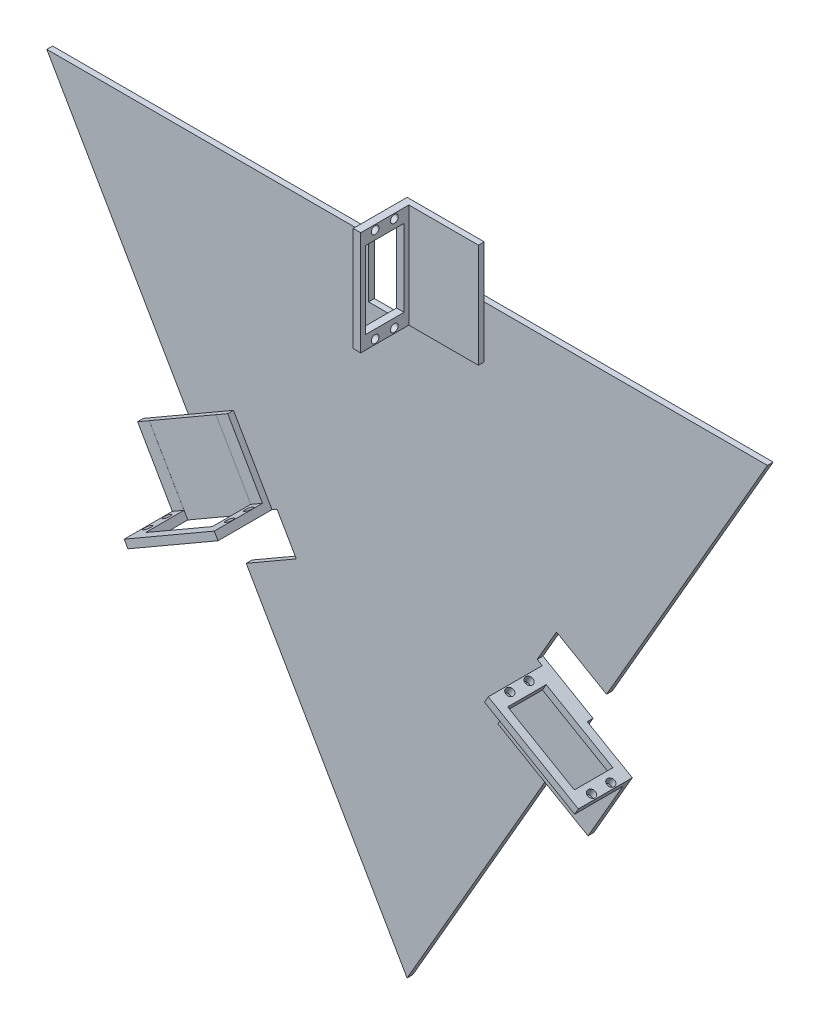
SolidWorks part; units mm, degrees
ref_plane "Front Plane" through (0, 0, 0) normal (0, 0, 1) x (1, 0, 0)
ref_plane "Top Plane" through (0, 0, 0) normal (0, 1, 0) x (1, 0, 0)
ref_plane "Right Plane" through (0, 0, 0) normal (1, 0, 0) x (0, 0, -1)
sketch "Sketch2" plane through (0, 0, 0) normal (0, 0, 1) x (1, 0, 0)
  line L0 (0, 161.9468) -> (0, -161.9468) construction
  line L1 (-187, 161.9468) -> (187, 161.9468)
  line L2 (187, 161.9468) -> (0, -161.9468)
  line L3 (-187, 161.9468) -> (0, -161.9468)
  point P4 (0, 0)
  point P8 (0, 161.9468)
  dimension "D1" = 374
  dimension "D2" = 374
  dimension "D3" = 374
extrude "Boss-Extrude1" add sketch "Sketch2" along normal blind 3
sketch "Sketch4" plane through (0, 0, 3) normal (0, 0, 1) x (1, 0, 0)
  line L0 (0, 0) -> (-187, 161.9468) construction
  line L2 (0, 0) -> (0, -161.9468) construction
  line L3 (187, 161.9468) -> (0, -161.9468) construction
  line L4 (116.8827, -13.5) -> (96.8827, -48.141)
  line L6 (70.1173, 13.5) -> (116.8827, -13.5)
  line L7 (70.1173, 13.5) -> (50.1173, -21.141)
  line L8 (73.5, -34.641) -> (28.9418, -111.818) construction
  line L9 (50.1173, -21.141) -> (96.8827, -48.141)
  line L10 (0, 0) -> (187, 161.9468) construction
  line L11 (0, -161.9468) -> (-187, 161.9468) construction
  line L12 (-116.8827, -13.5) -> (-136.8827, 21.141)
  line L13 (-70.1173, 13.5) -> (-116.8827, -13.5)
  line L14 (-70.1173, 13.5) -> (-90.1173, 48.141)
  line L15 (-90.1173, 48.141) -> (-136.8827, 21.141)
  line L20 (-187, 161.9468) -> (187, 161.9468) construction
  line L21 (40, 134.9468) -> (0, 134.9468)
  line L22 (40, 188.9468) -> (40, 134.9468)
  line L23 (40, 188.9468) -> (0, 188.9468)
  line L24 (0, 188.9468) -> (0, 134.9468)
  point P13 (-93.5, 0)
  point P16 (93.5, 0)
  point P18 (93.5, 0)
  point P25 (-93.5, 0)
  point P29 (0, 161.9468)
  point P30 (0, 161.9468)
  dimension "D1" = 40
  dimension "D2" = 54
  dimension "D3" = 54
  dimension "D4" = 40
  dimension "D5" = 54
  dimension "D6" = 40
extrude "Boss-Extrude2" add sketch "Sketch4" along normal blind 3
sketch "Sketch11" plane through (0, 0, 6) normal (0, 0, 1) x (1, 0, 0)
  line L0 (93.5, 0) -> (73.5, -34.641) construction
  line L1 (116.8827, -13.5) -> (70.1173, 13.5) construction
  line L2 (116.8827, -13.5) -> (114.9327, -16.8775)
  line L3 (96.8827, -48.141) -> (116.8827, -13.5) construction
  line L4 (114.9327, -16.8775) -> (68.1673, 10.1225)
  line L5 (70.1173, 13.5) -> (50.1173, -21.141) construction
  line L6 (68.1673, 10.1225) -> (70.1173, 13.5)
  line L7 (70.1173, 13.5) -> (50.1173, -21.141) construction
  line L8 (70.1173, 13.5) -> (116.8827, -13.5)
  line L9 (-93.5, 0) -> (-113.5, 34.641) construction
  line L10 (-116.8827, -13.5) -> (-70.1173, 13.5) construction
  line L11 (-90.1173, 48.141) -> (-136.8827, 21.141) construction
  line L12 (-116.8827, -13.5) -> (-118.8327, -10.1225)
  line L13 (-136.8827, 21.141) -> (-116.8827, -13.5) construction
  line L14 (-118.8327, -10.1225) -> (-72.0673, 16.8775)
  line L15 (-70.1173, 13.5) -> (-90.1173, 48.141) construction
  line L16 (-72.0673, 16.8775) -> (-70.1173, 13.5)
  line L17 (-70.1173, 13.5) -> (-116.8827, -13.5)
  line L18 (0, 188.9468) -> (0, 134.9468)
  line L19 (0, 134.9468) -> (3.9, 134.9468)
  line L20 (0, 134.9468) -> (40, 134.9468) construction
  line L21 (3.9, 134.9468) -> (3.9, 188.9468)
  line L22 (40, 188.9468) -> (0, 188.9468) construction
  line L23 (3.9, 188.9468) -> (0, 188.9468)
  dimension "D1" = 3.9
  dimension "D2" = 3.9
  dimension "D3" = 3.9
extrude "Boss-Extrude3" add sketch "Sketch11" along normal blind 25
sketch "Sketch12" plane through (-23.375, 40.4867, 0) normal (0.5, -0.866, 0) x (0.866, 0.5, 0)
  line L0 (-107.9734, 15.9815) -> (-53.9734, 15.9815) construction
  line L1 (-53.9734, 31) -> (-53.9734, 3) construction
  line L2 (-107.9734, 31) -> (-107.9734, 3) construction
  line L3 (-100.9734, 25.9815) -> (-60.9734, 25.9815)
  line L4 (-100.9734, 25.9815) -> (-100.9734, 5.9815)
  line L5 (-100.9734, 5.9815) -> (-60.9734, 5.9815)
  line L6 (-60.9734, 25.9815) -> (-60.9734, 5.9815)
  line L7 (-100.9734, 25.9815) -> (-60.9734, 5.9815) construction
  line L8 (-100.9734, 5.9815) -> (-60.9734, 25.9815) construction
  circle A0 centre (-56.4734, 10.9815) radius 2
  circle A1 centre (-56.4734, 20.9815) radius 2
  circle A2 centre (-105.4734, 20.9815) radius 2
  circle A3 centre (-105.4734, 10.9815) radius 2
  point P8 (-80.9734, 15.9815)
  point P14 (-80.9734, 15.9815)
  dimension "D3" = 4
  dimension "D4" = 2.5
  dimension "D5" = 2.5
  dimension "D6" = 2.5
  dimension "D7" = 2.5
  dimension "D8" = 5
  dimension "D9" = 5
  dimension "D10" = 5
  dimension "D1" = 40
  dimension "D2" = 20
  dimension "D11" = 5
sketch "Sketch13" plane through (23.375, 40.4867, 0) normal (0.5, 0.866, 0) x (0.866, -0.5, 0)
  line L0 (53.9734, -17) -> (107.9734, -17) construction
  line L1 (60.9734, -7) -> (100.9734, -7)
  line L2 (60.9734, -7) -> (60.9734, -27)
  line L3 (60.9734, -27) -> (100.9734, -27)
  line L4 (100.9734, -7) -> (100.9734, -27)
  line L5 (60.9734, -7) -> (100.9734, -27) construction
  line L6 (60.9734, -27) -> (100.9734, -7) construction
  circle A0 centre (105.4734, -22) radius 2
  circle A1 centre (105.4734, -12) radius 2
  circle A2 centre (56.4734, -12) radius 2
  circle A3 centre (56.4734, -22) radius 2
  point P3 (80.9734, -17)
  point P8 (80.9734, -17)
  dimension "D1" = 5
  dimension "D3" = 4.5
  dimension "D4" = 4.5
  dimension "D5" = 4.5
  dimension "D6" = 5
  dimension "D7" = 5
  dimension "D8" = 4.5
  dimension "D2" = 5
sketch "Sketch16" plane through (3.9, 0, 0) normal (1, 0, 0) x (0, 0, -1)
  line L0 (-18.5, 134.9468) -> (-18.5, 188.9468) construction
  line L1 (-28.5, 141.9468) -> (-28.5, 181.9468)
  line L2 (-28.5, 141.9468) -> (-8.5, 141.9468)
  line L3 (-8.5, 141.9468) -> (-8.5, 181.9468)
  line L4 (-28.5, 181.9468) -> (-8.5, 181.9468)
  line L5 (-28.5, 141.9468) -> (-8.5, 181.9468) construction
  line L6 (-8.5, 141.9468) -> (-28.5, 181.9468) construction
  line L9 (-31, 134.9468) -> (-31, 188.9468) construction
  circle A0 centre (-13.5, 186.4468) radius 2
  circle A1 centre (-23.5, 186.4468) radius 2
  circle A2 centre (-23.5, 137.4468) radius 2
  circle A3 centre (-13.5, 137.4468) radius 2
  point P3 (-18.5, 161.9468)
  point P8 (-18.5, 161.9468)
  dimension "D1" = 4.5
  dimension "D2" = 5
  dimension "D4" = 4.5
  dimension "D5" = 4.5
  dimension "D6" = 4.5
  dimension "D7" = 5
  dimension "D3" = 5
  dimension "D8" = 5
extrude "Cut-Extrude2" cut sketch "Sketch16" against normal through all both and the other way through all
extrude "Cut-Extrude3" cut sketch "Sketch13" against normal through all both and the other way through all
extrude "Cut-Extrude4" cut sketch "Sketch12" against normal through all both and the other way through all
sketch "Sketch17" plane through (0, 0, 3) normal (0, 0, 1) x (1, 0, 0)
  line L1 (-116.8827, -13.5) -> (-70.1173, 13.5) construction
  line L2 (-93.5, 0) -> (0, -161.9468) construction
  line L3 (-93.5, 0) -> (-67.5192, 15)
  line L4 (-67.5192, 15) -> (-57.5192, -2.3205)
  line L5 (-57.5192, -2.3205) -> (-83.5, -17.3205)
  line L6 (93.5, 0) -> (103.5, 17.3205)
  line L7 (93.5, 0) -> (187, 161.9468) construction
  line L8 (103.5, 17.3205) -> (77.5192, 32.3205)
  line L9 (77.5192, 32.3205) -> (67.5192, 15)
  line L12 (0, 131.9468) -> (-20, 131.9468)
  line L13 (-20, 131.9468) -> (-20, 161.9468)
  line L14 (0, 161.9468) -> (-187, 161.9468) construction
  line L15 (-20, 161.9468) -> (0, 161.9468)
  line L16 (0, 188.9468) -> (0, 134.9468) construction
  line L17 (0, 161.9468) -> (0, 131.9468)
  line L18 (-83.5, -17.3205) -> (-93.5, 0)
  line L19 (67.5192, 15) -> (93.5, 0)
  dimension "D1" = 20
  dimension "D2" = 20
  dimension "D3" = 30
  dimension "D4" = 30
  dimension "D5" = 20
  dimension "D6" = 30
extrude "Cut-Extrude5" cut sketch "Sketch17" against normal mid plane 160
